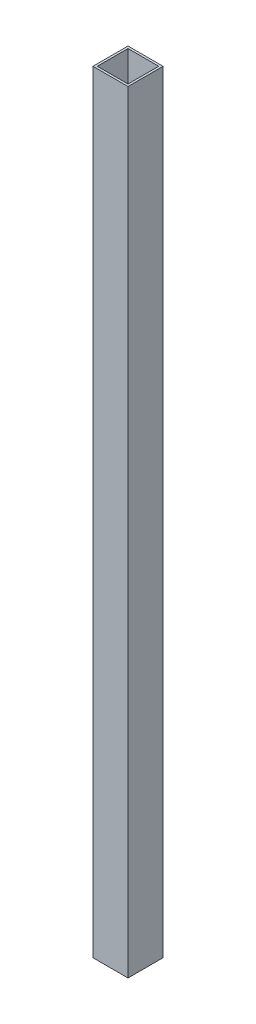
SolidWorks part; units mm, degrees
material "6061 Alloy"
ref_plane "Front Plane" through (0, 0, 0) normal (0, 0, 1) x (1, 0, 0)
ref_plane "Top Plane" through (0, 0, 0) normal (0, 1, 0) x (1, 0, 0)
ref_plane "Right Plane" through (0, 0, 0) normal (1, 0, 0) x (0, 0, -1)
sketch "Sketch1" plane through (0, 0, 0) normal (0, 1, 0) x (1, 0, 0)
  line L1 (-11.1125, -11.1125) -> (11.1125, -11.1125)
  line L2 (-11.1125, -11.1125) -> (-11.1125, 11.1125)
  line L3 (-11.1125, 11.1125) -> (11.1125, 11.1125)
  line L4 (11.1125, -11.1125) -> (11.1125, 11.1125)
  line L5 (-11.1125, -11.1125) -> (11.1125, 11.1125) construction
  line L6 (-11.1125, 11.1125) -> (11.1125, -11.1125) construction
  line L7 (-12.7, -12.7) -> (12.7, -12.7)
  line L8 (-12.7, -12.7) -> (-12.7, 12.7)
  line L9 (-12.7, 12.7) -> (12.7, 12.7)
  line L10 (12.7, -12.7) -> (12.7, 12.7)
  line L11 (-12.7, -12.7) -> (12.7, 12.7) construction
  line L12 (-12.7, 12.7) -> (12.7, -12.7) construction
  point P0 (0, 0)
  point P6 (0, 0)
  dimension "D1" = 25.4
  dimension "D2" = 1.5875
extrude "Boss-Extrude1" add sketch "Sketch1" along normal blind 558.8
